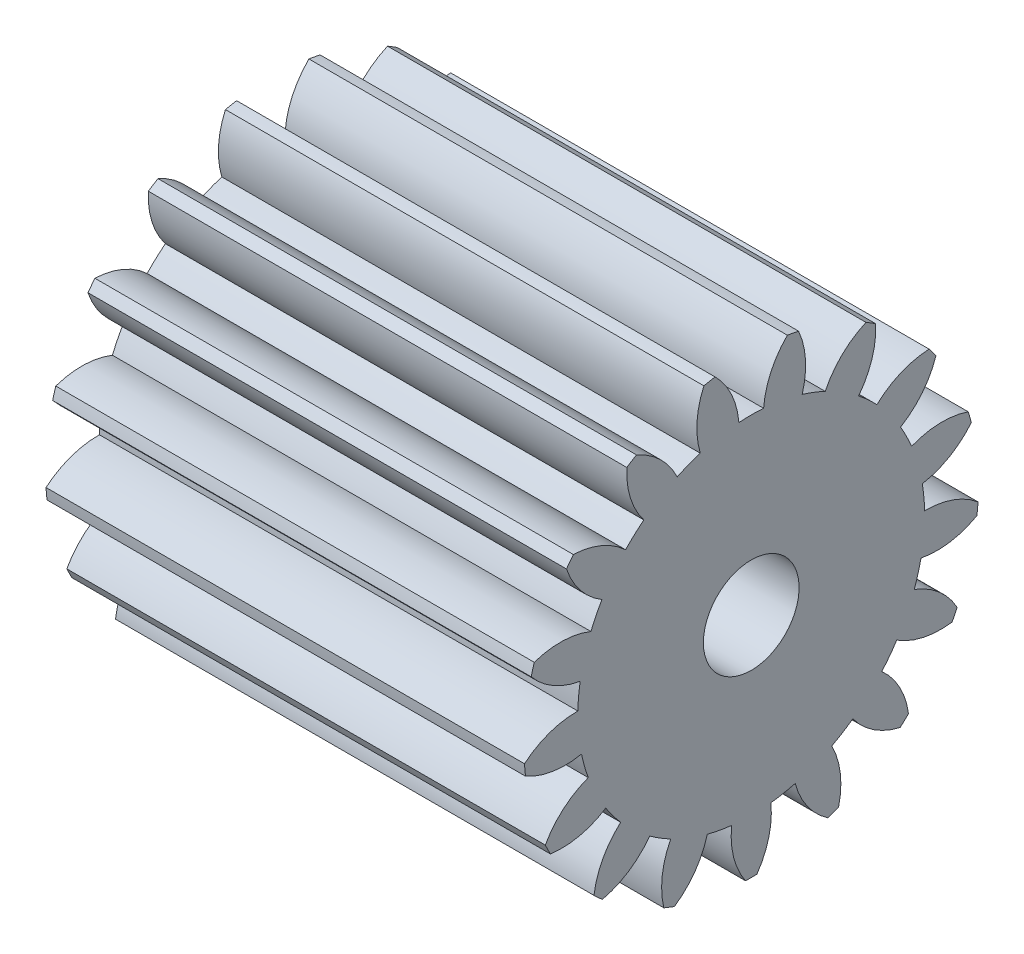
SolidWorks part; units mm, degrees
material "1.0035 (S185)"
ref_plane "Plane1" through (0, 0, 0) normal (0, 0, 1) x (1, 0, 0)
ref_plane "Plane2" through (0, 0, 0) normal (0, 1, 0) x (1, 0, 0)
ref_plane "Plane3" through (0, 0, 0) normal (1, 0, 0) x (0, 0, -1)
sketch "HoldingSke" plane through (0, 0, 0) normal (0, 1, 0) x (1, 0, 0)
  line L0 (0, 0) -> (1.9126, -0.5847)
  line L1 (-15, 0) -> (100, 0) construction
  line L2 (0, 0) -> (-2.1039, 2.3779)
  line L3 (0, 0) -> (-11.863, 4.5341)
  line L4 (0, 0) -> (8.2586, 2.5249)
  line L5 (0, 0) -> (-46.8476, -17.4728)
  line L6 (0, 0) -> (-8.2896, -5.593)
  line L7 (-2.1039, 2.3779) -> (8.6586, 51.2059)
  line L8 (-76.2, 54.61) -> (-75.9, 54.61)
  line L9 (-71.009, 38.7566) -> (-53.1078, 45.2721)
  line L10 (-76.2, 71.12) -> (104.1128, 71.12)
  line L11 (0, 0) -> (-10, 0)
  line L12 (-76.2, 101.6) -> (-76.181, 101.6)
  line L13 (24.9733, 27.94) -> (52.9518, 28.4284)
  line L14 (24.9733, 27.94) -> (24.9743, 27.94)
  line L15 (24.9733, 27.94) -> (100.4006, 29.5858)
  line L16 (-63.627, -0.5) -> (-12.827, -0.5)
  circle A0 centre (0, 0) radius 1
  circle A1 centre (0, 0) radius 3.624
  circle A2 centre (0, 0) radius 37.5
  circle A3 centre (0, 0) radius 1
  dimension "MHD" = 7.248
  dimension "Hub_dia" = 75
  dimension "Bore" = 2
  dimension "MBD" = 2
  dimension "Num_teeth" = 17
  dimension "Pitch_radius" = 180.3128
  dimension "Pitch" = 2
  dimension "Width" = 10
  dimension "Overall_len" = 50
  dimension "Show_teeth" = 17
  dimension "Thickness" = 10
  dimension "OAL" = 50.0001
  dimension "T_dim" = 0.3
  dimension "Ap" = 20
  dimension "H" = 19.05
  dimension "Backlash" = 0.019
  dimension "Addendum_fac" = 1
  dimension "Dedendum_fac" = 1.25
  dimension "Clearance_fac" = 0.25
  dimension "Dedendum_add" = 0.001
  dimension "Module" = 0.5
sketch "BasProSke" plane through (0, 0, 0) normal (0, 1, 0) x (1, 0, 0)
  line L0 (-10, 0) -> (60, 0) construction
  line L1 (0, 0) -> (0, 4.75)
  line L2 (0, 0) -> (10, 0)
  line L3 (10, 0) -> (10, 4.75)
  line L4 (10, 4.75) -> (0, 4.75)
  dimension "Diameter" = 9.5
  dimension "Thickness" = 10
revolve "Base-Revolve" add sketch "BasProSke" angle 360 about L0
sketch "TooCutSke" plane through (0, 0, 0) normal (1, 0, 0) x (0, 0, -1)
  line L1 (0, 0) -> (0, 107) construction
  line L2 (0, 0) -> (-0.4254, 4.2287) construction
  line L3 (0, 0) -> (-1.5563, 8.3254) construction
  line L4 (-0.4254, 4.2287) -> (-0.7781, 4.1627) construction
  arc A0 (0.2584, 3.6148) -> (-0.2584, 3.6148) centre (0, 0) ccw
  arc A1 (0.7779, 4.7116) -> (-0.7779, 4.7116) centre (0, 0) ccw
  circle A2 centre (0, 0) radius 4.25 construction
  circle A3 centre (0, 0) radius 3.9937 construction
  arc A4 (-0.2584, 3.6148) -> (-0.7779, 4.7116) centre (-1.9533, 3.4834) ccw
  arc A5 (0.7779, 4.7116) -> (0.2584, 3.6148) centre (1.9533, 3.4834) ccw
  dimension "Root_dia" = 7.248
  dimension "Overcut_dia" = 9.5508
  dimension "Pitch_dia" = 8.5
  dimension "Base_dia" = 7.9874
  dimension "Flank_rad" = 1.7
  dimension "Half_ang" = 10.588
  dimension "Half_CT" = 0.3589
extrude "ToothCut" cut sketch "TooCutSke" along normal through all
fillet "Breaks" [suppressed] radius 0.01
fillet "RootFillets" [suppressed] radius 0.126
pattern_circular "TeethCuts" count 17 every 21.176 about axis through (-10, 0, 0) along (1, 0, 0) of "ToothCut", "RootFillets", "Breaks"
sketch "HubNeaOneSke" plane through (0, 0, 0) normal (-1, 0, 0) x (0, 0, 1)
  circle A0 centre (0, 0) radius 3.624
  dimension "Diameter" = 7.248
extrude "HubNearOne" [suppressed] add sketch "HubNeaOneSke" along normal blind 40.0001
sketch "HubNeaBotSke" plane through (0, 0, 0) normal (-1, 0, 0) x (0, 0, 1)
  circle A0 centre (0, 0) radius 3.624
  dimension "Diameter" = 7.248
extrude "HubNearBoth" [suppressed] add sketch "HubNeaBotSke" along normal blind 20
ref_plane "FarPln" through (10, 0, 0) normal (1, 0, 0) x (0, 0, -1)
sketch "HubFarSke" plane through (10, 0, 0) normal (1, 0, 0) x (0, 0, -1)
  circle A0 centre (0, 0) radius 3.624
  dimension "Diameter" = 7.248
extrude "HubFar" [suppressed] add sketch "HubFarSke" along normal blind 20
sketch "BorSke" plane through (0, 0, 0) normal (1, 0, 0) x (0, 0, -1)
  circle A0 centre (0, 0) radius 1
  dimension "Diameter" = 2
extrude "Bore" cut sketch "BorSke" along normal mid plane 100.0001
sketch "KeySke" plane through (0, 0, 0) normal (1, 0, 0) x (0, 0, -1)
  line L0 (-0.4, 0) -> (-0.4, 1.3)
  line L1 (-0.4, 1.3) -> (0.4, 1.3)
  line L2 (0.4, 1.3) -> (0.4, 0)
  line L3 (0, 0) -> (0, 34) construction
  line L4 (-0.4, 0) -> (0.4, 0)
  dimension "Offset" = 1.3
  dimension "Width" = 0.8
extrude "Keyway" [suppressed] cut sketch "KeySke" along normal mid plane 100.0001
pattern_circular "Keyway2" [suppressed] count 2 every 90 about axis through (-10, 0, 0) along (1, 0, 0)
equation "' \"Module@HoldingSke\" = 6.35"
equation "' \"Num_teeth@HoldingSke\" = 12"
equation "' \"Ap@HoldingSke\" =  20"
equation "' \"Width@HoldingSke\" = 0.5 * 25.4"
equation "' \"Hub_dia@HoldingSke\"= 1 * 25.4"
equation "' \"Overall_len@HoldingSke\" = 1.0 * 25.4"
equation "' \"Bore@HoldingSke\" = 0.75 * 25.4"
equation "' \"T_dim@HoldingSke\" = 0.1 * 25.4"
equation "' \"Width@KeySke\" = 0.25 * 25.4"
equation "' \"Show_teeth@HoldingSke\" = 13"
equation "' \"Backlash@HoldingSke\" = 0.009 * 25.4"
equation "' \"Addendum_fac@HoldingSke\" = 1.0"
equation "' \"Dedendum_fac@HoldingSke\" = 1.25"
equation "' \"Dedendum_add@HoldingSke\" = 0.00005 * 25.4"
equation "' \"Clearance_fac@HoldingSke\" = 0.25"
equation "\"Pitch@HoldingSke\" = 1 / \"Module@HoldingSke\""
equation "\"Overcut_dia@TooCutSke\" = (\"Num_teeth@HoldingSke\" + 2 * \"Addendum_fac@HoldingSke\") / \"Pitch@HoldingSke\" + 0.002 * 25.4"
equation "\"Pitch_dia@TooCutSke\" = \"Num_teeth@HoldingSke\" / \"Pitch@HoldingSke\""
equation "\"Base_dia@TooCutSke\" = \"Num_teeth@HoldingSke\" / \"Pitch@HoldingSke\" * cos((\"Ap@HoldingSke\"  * 3.14159265 / 180))"
equation "\"Root_dia@TooCutSke\" = (\"Num_teeth@HoldingSke\" + 2) / \"Pitch@HoldingSke\" - 2 * (\"Addendum_fac@HoldingSke\" + \"Dedendum_fac@HoldingSke\") / \"Pitch@HoldingSke\" - \"Dedendum_add@HoldingSke\" * 2"
equation "\"Half_ang@TooCutSke\" = 180 / \"Num_teeth@HoldingSke\""
equation "\"Half_CT@TooCutSke\" = \"Num_teeth@HoldingSke\" / \"Pitch@HoldingSke\" * sin((3.14159265 / 2 / \"Num_teeth@HoldingSke\")) / 2 - 7 * \"Backlash@HoldingSke\" / 4"
equation "\"Flank_rad@TooCutSke\" = \"Num_teeth@HoldingSke\" / \"Pitch@HoldingSke\" / 5"
equation "\"Radius@RootFillets\" = \"Clearance_fac@HoldingSke\" / \"Pitch@HoldingSke\" + \"Dedendum_add@HoldingSke\""
equation "\"Break_rad@Breaks\" = 0.02 / \"Pitch@HoldingSke\""
equation "\"Thickness@HoldingSke\" = \"Width@HoldingSke\""
equation "\"OAL@HoldingSke\" = \"Thickness@HoldingSke\""
equation "\"MHD@HoldingSke\" = (\"Num_teeth@HoldingSke\" + 2) / \"Pitch@HoldingSke\" - 2 * (\"Addendum_fac@HoldingSke\" + \"Dedendum_fac@HoldingSke\")  / \"Pitch@HoldingSke\" - \"Dedendum_add@HoldingSke\" * 2"
equation "\"MBD@HoldingSke\" = (\"Num_teeth@HoldingSke\" + 2) / \"Pitch@HoldingSke\" - 2 * (\"Addendum_fac@HoldingSke\" + \"Dedendum_fac@HoldingSke\")  / \"Pitch@HoldingSke\" - \"Dedendum_add@HoldingSke\" * 2 - 0.002 * 25.4"
equation "\"MHD@HoldingSke\" = ((sgn( \"MHD@HoldingSke\" - \"Hub_dia@HoldingSke\" )-1)*( \"MHD@HoldingSke\" - \"Hub_dia@HoldingSke\" ))/-2+ \"Hub_dia@HoldingSke\""
equation "\"MBD@HoldingSke\" = ((sgn( \"MBD@HoldingSke\" - \"Bore@HoldingSke\" )-1)*( \"MBD@HoldingSke\" - \"Bore@HoldingSke\" ))/-2+ \"Bore@HoldingSke\""
equation "\"OAL@HoldingSke\" = ((sgn( \"OAL@HoldingSke\" - \"Overall_len@HoldingSke\" )+1)*( \"OAL@HoldingSke\" - \"Overall_len@HoldingSke\" ))/2 + \"Overall_len@HoldingSke\" + 0.000002 * 25.4"
equation "\"Num_teeth@TeethCuts\" = int( \"Show_teeth@HoldingSke\" ) + 1"
equation "\"Num_teeth@TeethCuts\" = ((sgn( \"Num_teeth@TeethCuts\" - \"Num_teeth@HoldingSke\" )-1)*( \"Num_teeth@TeethCuts\" - \"Num_teeth@HoldingSke\" ))/-2+ \"Num_teeth@HoldingSke\""
equation "\"Num_teeth@TeethCuts\" = ((sgn( \"Num_teeth@TeethCuts\" - 2.0)+1)*( \"Num_teeth@TeethCuts\" - 2.0))/2 +2.0"
equation "\"Angle@TeethCuts\" = 360.0 / \"Num_teeth@HoldingSke\""
equation "\"Diameter@BasProSke\" = (\"Num_teeth@HoldingSke\" + 2 * \"Addendum_fac@HoldingSke\") / \"Pitch@HoldingSke\""
equation "\"Thickness@BasProSke\"  = \"Thickness@HoldingSke\""
equation "' \"Fillet_rad@BasProSke\" =  \"Thickness@HoldingSke\" * 0.05"
equation "\"MHD@HoldingSke\" = ((sgn( \"MHD@HoldingSke\" - \"Root_dia@TooCutSke\" )-1)*( \"MHD@HoldingSke\" - \"Root_dia@TooCutSke\" ))/-2+ \"Root_dia@TooCutSke\""
equation "\"Diameter@HubNeaOneSke\" = \"MHD@HoldingSke\""
equation "\"Length@HubNearOne\" = \"OAL@HoldingSke\" - \"Thickness@BasProSke\""
equation "\"Diameter@HubNeaBotSke\" = \"MHD@HoldingSke\""
equation "\"Length@HubNearBoth\" = ( \"OAL@HoldingSke\" - \"Thickness@BasProSke\" ) / 2.0"
equation "\"Thickness@FarPln\" = \"Thickness@BasProSke\""
equation "\"Diameter@HubFarSke\" = \"MHD@HoldingSke\""
equation "\"Length@HubFar\" = ( \"OAL@HoldingSke\" - \"Thickness@BasProSke\" ) / 2.0"
equation "\"Diameter@BorSke\" = \"MBD@HoldingSke\""
equation "\"D1@Bore\" = \"OAL@HoldingSke\" * 2.0"
equation "\"D1@Keyway\" = \"OAL@HoldingSke\" * 2.0"
equation "\"Offset@KeySke\" = \"T_dim@HoldingSke\" + \"MBD@HoldingSke\" / 2.0"
